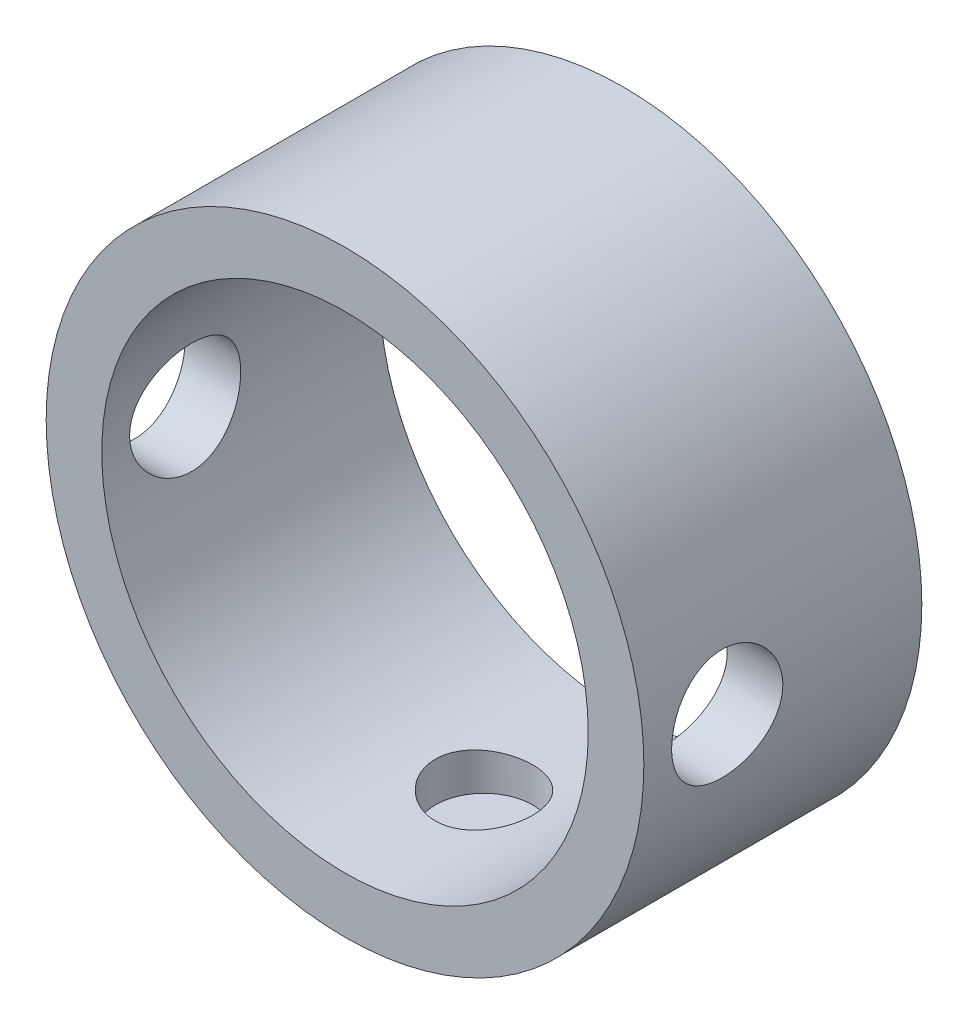
SolidWorks part; units mm, degrees
ref_plane "Plan de face" through (0, 0, 0) normal (0, 0, 1) x (1, 0, 0)
ref_plane "Plan de dessus" through (0, 0, 0) normal (0, 1, 0) x (1, 0, 0)
ref_plane "Plan de droite" through (0, 0, 0) normal (1, 0, 0) x (0, 0, -1)
sketch "Esquisse1" plane through (0, 0, 0) normal (0, 0, 1) x (1, 0, 0)
  circle A0 centre (0, 0) radius 8.75
  circle A1 centre (0, 0) radius 10.75
  dimension "D1" = 2
  dimension "D2" = 17.5
extrude "Boss.-Extru.1" add sketch "Esquisse1" along normal blind 10
sketch "Esquisse2" plane through (0, 0, 0) normal (0, 1, 0) x (1, 0, 0)
  circle A0 centre (0, -5) radius 1.75
  dimension "D1" = 0
  dimension "D3" = 3.5
  dimension "D2" = 5
extrude "Enlèv. mat.-Extru.1" cut sketch "Esquisse2" against normal blind 10
sketch "Esquisse3" plane through (0, 0, 0) normal (1, 0, 0) x (0, 0, -1)
  circle A0 centre (-7, 0) radius 2
  dimension "D1" = 7
  dimension "D2" = 4
  dimension "D3" = 0
extrude "Enlèv. mat.-Extru.2" cut sketch "Esquisse3" against normal mid plane 30
